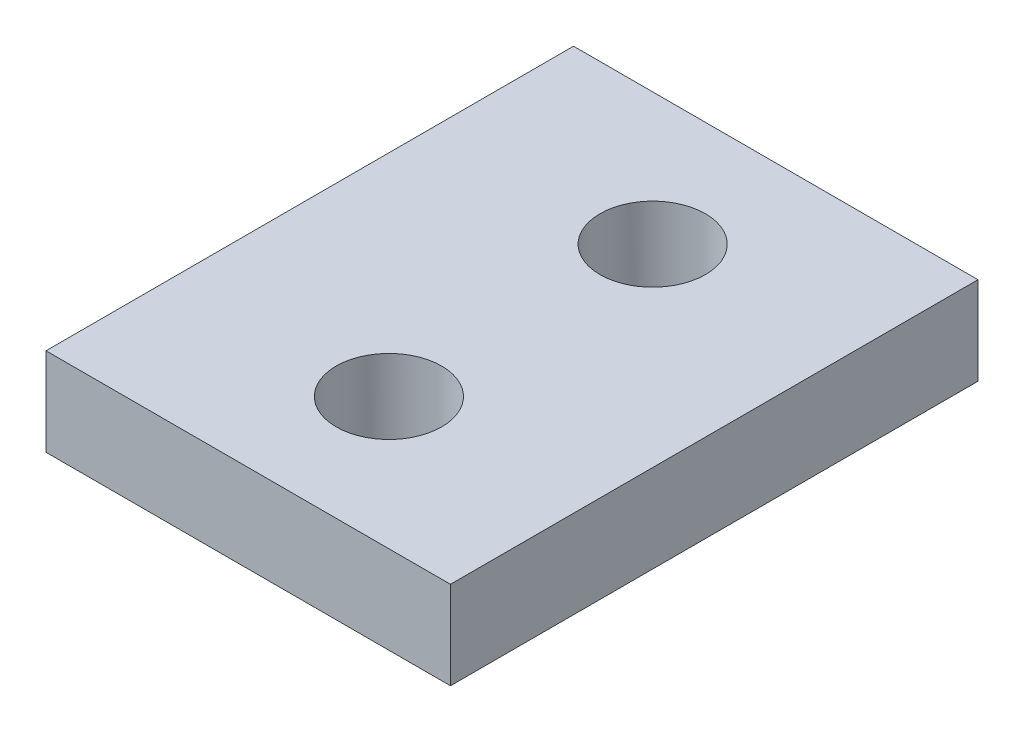
SolidWorks part; units mm, degrees
ref_plane "Ebene vorne" through (0, 0, 0) normal (0, 0, 1) x (1, 0, 0)
ref_plane "Ebene oben" through (0, 0, 0) normal (0, 1, 0) x (1, 0, 0)
ref_plane "Ebene rechts" through (0, 0, 0) normal (1, 0, 0) x (0, 0, -1)
sketch "Side" plane through (0, 0, 0) normal (0, 0, 1) x (1, 0, 0)
  line L1 (-65, -11) -> (-42, -11)
  line L2 (-65, -11) -> (-65, -16)
  line L3 (-65, -16) -> (-42, -16)
  line L4 (-42, -11) -> (-42, -16)
sketch "Width" plane through (0, 0, 0) normal (1, 0, 0) x (0, 0, -1)
  line L0 (15, 0) -> (-15, 0)
  point P8 (0, 0)
sketch "Skizze3" plane through (0, 0, 0) normal (0, 0, 1) x (1, 0, 0)
  line L1 (-65, -11) -> (-42, -11)
  line L2 (-65, -11) -> (-65, -16)
  line L3 (-65, -16) -> (-42, -16)
  line L4 (-42, -11) -> (-42, -16)
extrude "Aufsatz-Linear austragen1" add sketch "Skizze3" along normal up to vertex (15 mm away) and the other way up to vertex (15 mm away) up to point (0, 0, 15) other way up to point (0, 0, -15)
sketch "Skizze4" plane through (0, 0, 0) normal (0, 1, 0) x (1, 0, 0)
  line L1 (0, 0) -> (30.9843, 0) construction
  line L4 (-65, -15) -> (65, -15)
  line L5 (-65, -15) -> (-65, 15)
  line L6 (-65, 15) -> (65, 15)
  line L7 (65, -15) -> (65, 15)
  line L8 (-65, -15) -> (65, 15) construction
  line L9 (-65, 15) -> (65, -15) construction
  circle A0 centre (53, -7.5) radius 1.65
  circle A1 centre (53, 7.5) radius 1.65
  circle A2 centre (-53, 7.5) radius 1.65
  circle A3 centre (-53, -7.5) radius 1.65
  point P8 (0, 0)
sketch "Skizze5" plane through (0, 0, 0) normal (0, 1, 0) x (1, 0, 0)
  circle A0 centre (-53, 7.5) radius 3
  circle A1 centre (-53, -7.5) radius 3
extrude "Schnitt-Linear austragen1" cut sketch "Skizze5" against normal up to surface (16 mm away) up to face at (-53.5, -16, 0)
